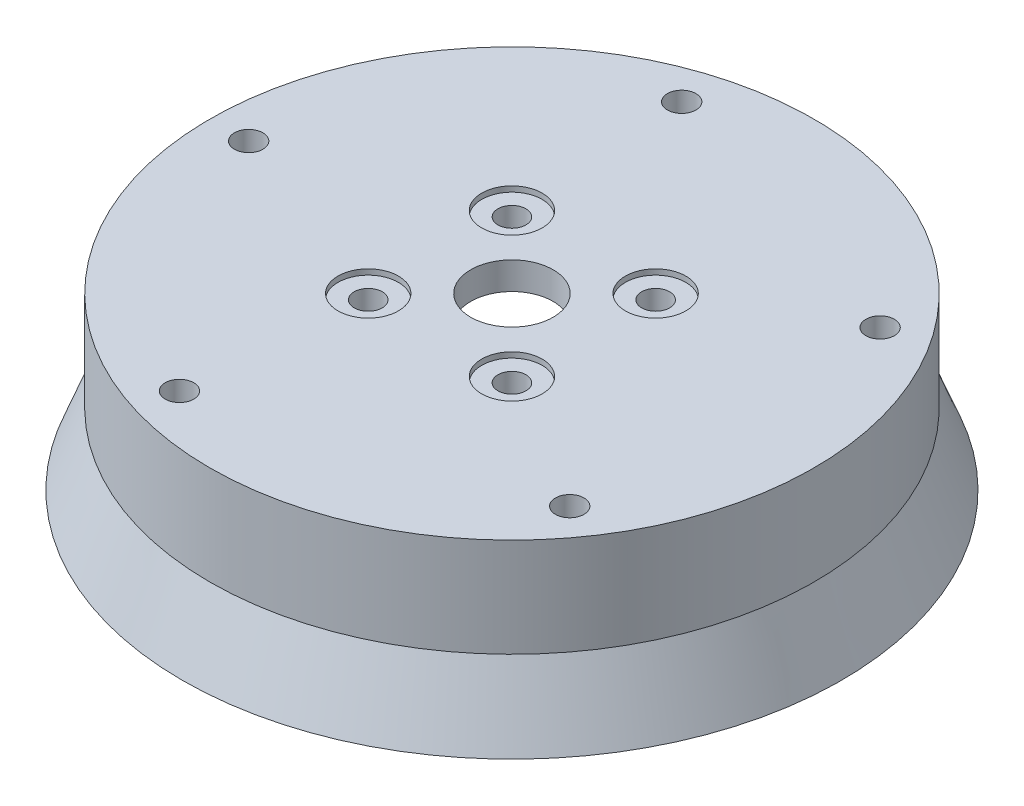
SolidWorks part; units mm, degrees
ref_plane "Front Plane" through (0, 0, 0) normal (0, 0, 1) x (1, 0, 0)
ref_plane "Top Plane" through (0, 0, 0) normal (0, 1, 0) x (1, 0, 0)
ref_plane "Right Plane" through (0, 0, 0) normal (1, 0, 0) x (0, 0, -1)
sketch "Sketch1" plane through (0, 0, 0) normal (0, 0, 1) x (1, 0, 0)
  line L0 (-60, -31) -> (-55, -18)
  line L1 (-60, -31) -> (-78.2035, -31) construction
  line L2 (-55, -18) -> (-55, 0)
  line L3 (-55, 0) -> (-7.5, 0)
  line L4 (-7.5, 0) -> (-7.5, -5)
  line L5 (-7.5, -5) -> (-26.5, -5)
  line L6 (0, 0) -> (0, -46.697) construction
  line L9 (-26.5, -6.0045) -> (-26.5, -5)
  line L11 (-60, -31) -> (-52, -31)
  line L12 (-52, -31) -> (-26.5, -6.0045)
  point P3 (-23.6667, -4)
  point P9 (-27.1233, -6.0045)
  point P12 (-26.5, -6.074)
  point P16 (-30.0377, -7.8226)
  point P17 (-26.5, -6.3181)
  dimension "D2" = 15
  dimension "D3" = 110
  dimension "D4" = 18
  dimension "D5" = 5
  dimension "D6" = 13
  dimension "D7" = 8
  dimension "D9" = 53
  dimension "D11" = 1.0045
  dimension "D12" = 120
revolve "Revolve1" add sketch "Sketch1" angle 360 about L6
sketch "Sketch2" plane through (0, 0, 0) normal (0, 1, 0) x (1, 0, 0)
  circle A0 centre (-48, 0.0692) radius 2.5975
  circle A1 centre (-14.7669, 45.6721) radius 2.5975
  circle A2 centre (38.8735, 28.1576) radius 2.5975
  circle A3 centre (38.7921, -28.2697) radius 2.5975
  circle A4 centre (-14.8987, -45.6293) radius 2.5975
  point P3 (0, 0)
  dimension "D1" = 5
extrude "Cut-Extrude1" cut sketch "Sketch2" against normal through all
sketch "Sketch3" plane through (0, -31, 0) normal (0, -1, 0) x (1, 0, 0)
  circle A0 centre (-48, -0.0692) radius 4
  circle A2 centre (-14.8987, 45.6293) radius 4
  circle A3 centre (38.7921, 28.2697) radius 4
  circle A4 centre (38.8735, -28.1576) radius 4
  circle A5 centre (-14.7669, -45.6721) radius 4
  circle A18 centre (-48, -0.0692) radius 2.5975 construction
  point P15 (0, 0)
  point P19 (0, 0)
  point P20 (76.3609, 23.3459)
  point P21 (0, 0)
  point P22 (66.7979, 20.4222)
  point P23 (0, 0)
  point P24 (66.7979, 20.4222)
  point P25 (0, 0)
  point P26 (7.1723, 2.1928)
  point P27 (0, 0)
  point P28 (7.1723, 2.1928)
  point P29 (0, 0)
  point P30 (25.3421, 7.7479)
  point P31 (0, 0)
  point P32 (25.3421, 7.7479)
  point P33 (0, 0)
  point P34 (27.2547, 8.3326)
  point P35 (0, 0)
  point P36 (27.2547, 8.3326)
  point P37 (0, 0)
  point P38 (50.5407, 15.4518)
  point P39 (0, 0)
  point P40 (68.7105, 21.0069)
  dimension "D1" = 8
  dimension "D2" = 5
extrude "Cut-Extrude3" cut sketch "Sketch3" against normal offset from surface (57 mm away) 4 from offset 30
sketch "Sketch4" plane through (0, 0, 0) normal (0, 1, 0) x (1, 0, 0)
  circle A0 centre (13.0815, 13.0815) radius 2.55
  circle A2 centre (13.0815, -13.0815) radius 2.55
  circle A3 centre (-13.0815, -13.0815) radius 2.55
  circle A4 centre (-13.0815, 13.0815) radius 2.55
  circle A5 centre (-48, 0.0692) radius 2.5975 construction
  point P11 (0, 0)
  dimension "D1" = 4
  dimension "D3" = 5.1
  dimension "D2" = 37
extrude "Cut-Extrude4" cut sketch "Sketch4" against normal through all
sketch "Sketch5" plane through (0, 0, 0) normal (0, 1, 0) x (1, 0, 0)
  circle A0 centre (13.0815, 13.0815) radius 5.5
  circle A1 centre (13.0815, -13.0815) radius 5.5
  circle A2 centre (-13.0815, -13.0815) radius 5.5
  circle A3 centre (-13.0815, 13.0815) radius 5.5
  circle A4 centre (13.0815, 13.0815) radius 2.55 construction
  circle A5 centre (13.0815, -13.0815) radius 2.55 construction
  circle A6 centre (-13.0815, -13.0815) radius 2.55 construction
  circle A7 centre (-13.0815, 13.0815) radius 2.55 construction
  dimension "D1" = 11
extrude "Cut-Extrude5" cut sketch "Sketch5" against normal offset from surface (1 mm away) 4 up to face at (-13.0815, -5, -15.6315)
